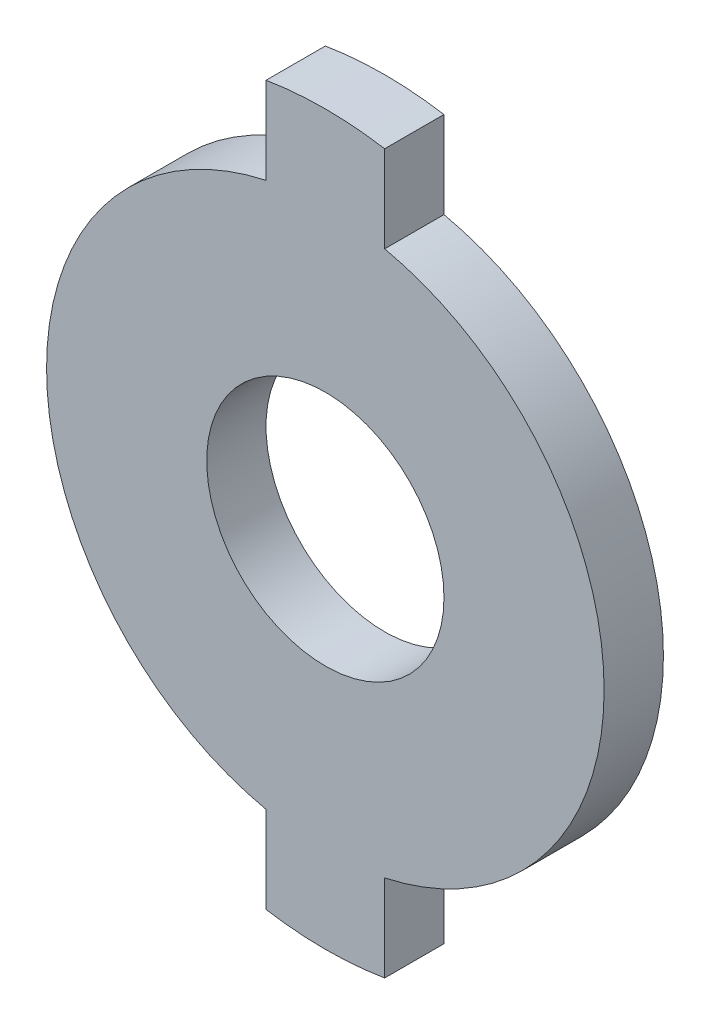
SolidWorks part; units mm, degrees
ref_plane "Front Plane" through (0, 0, 0) normal (0, 0, 1) x (1, 0, 0)
ref_plane "Top Plane" through (0, 0, 0) normal (0, 1, 0) x (1, 0, 0)
ref_plane "Right Plane" through (0, 0, 0) normal (1, 0, 0) x (0, 0, -1)
sketch "Sketch1" plane through (0, 0, 0) normal (0, 0, 1) x (1, 0, 0)
  line L2 (-5, -22.9619) -> (-5, -30.2698)
  line L4 (5, 30.2698) -> (5, 22.9619)
  line L6 (-5, 30.2698) -> (-5, 22.9619)
  line L7 (5, -22.9619) -> (5, -30.2698)
  arc A0 (-5, -30.2698) -> (5, -30.2698) centre (0, 0) ccw
  arc A2 (-5, 22.9619) -> (-5, -22.9619) centre (0, 0) ccw
  arc A3 (5, 30.2698) -> (-5, 30.2698) centre (0, 0) ccw
  arc A4 (5, -22.9619) -> (5, 22.9619) centre (0, 0) ccw
  dimension "D1" = 61.36
  dimension "D4" = 47
extrude "Boss-Extrude1" add sketch "Sketch1" along normal blind 5
sketch "Sketch2" plane through (0, 0, 5) normal (0, 0, 1) x (1, 0, 0)
  circle A0 centre (0, 0) radius 10
  dimension "D1" = 20
extrude "Cut-Extrude1" cut sketch "Sketch2" against normal blind 5
